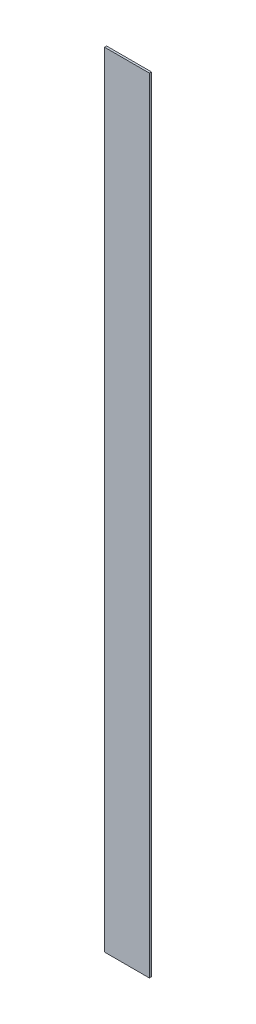
SolidWorks part; units mm, degrees
material "Cedar"
ref_plane "Front Plane" through (0, 0, 0) normal (0, 0, 1) x (1, 0, 0)
ref_plane "Top Plane" through (0, 0, 0) normal (0, 1, 0) x (1, 0, 0)
ref_plane "Right Plane" through (0, 0, 0) normal (1, 0, 0) x (0, 0, -1)
sketch "Sketch1" plane through (0, 0, 0) normal (0, 0, 1) x (1, 0, 0)
  line L0 (-43, -752) -> (43, -752)
  line L1 (43, -752) -> (43, 752)
  line L2 (43, 752) -> (-38, 752)
  line L3 (-80.1782, -752) -> (67.2915, -752) construction
  line L4 (-80.1782, -652) -> (67.2915, -652) construction
  line L5 (-80.1782, -552) -> (67.2915, -552) construction
  line L6 (-38, 752) -> (-43, 752)
  line L7 (-43, 752) -> (-43, -752)
  line L8 (-80.1782, -452) -> (67.2915, -452) construction
  line L9 (-80.1782, -352) -> (67.2915, -352) construction
  line L10 (-80.1782, -252) -> (67.2915, -252) construction
  line L11 (-80.1782, -152) -> (67.2915, -152) construction
  line L12 (-80.1782, -52) -> (67.2915, -52) construction
  line L13 (-80.1782, 48) -> (67.2915, 48) construction
  line L14 (-80.1782, 148) -> (67.2915, 148) construction
  line L15 (-80.1782, 248) -> (67.2915, 248) construction
  line L16 (-80.1782, 348) -> (67.2915, 348) construction
  line L17 (-80.1782, 448) -> (67.2915, 448) construction
  line L18 (-80.1782, 548) -> (67.2915, 548) construction
  line L19 (-80.1782, 648) -> (67.2915, 648) construction
  line L20 (-80.1782, 748) -> (67.2915, 748) construction
  line L21 (69.582, 752) -> (-94.7362, 752) construction
  line L22 (69.582, 652) -> (-94.7362, 652) construction
  line L23 (69.582, 552) -> (-94.7362, 552) construction
  line L24 (69.582, 452) -> (-94.7362, 452) construction
  line L25 (69.582, 352) -> (-94.7362, 352) construction
  line L26 (69.582, 252) -> (-94.7362, 252) construction
  line L27 (69.582, 152) -> (-94.7362, 152) construction
  line L28 (69.582, 52) -> (-94.7362, 52) construction
  line L29 (69.582, -48) -> (-94.7362, -48) construction
  line L30 (69.582, -148) -> (-94.7362, -148) construction
  line L31 (69.582, -248) -> (-94.7362, -248) construction
  line L32 (69.582, -348) -> (-94.7362, -348) construction
  line L33 (69.582, -448) -> (-94.7362, -448) construction
  line L34 (69.582, -548) -> (-94.7362, -548) construction
  line L35 (69.582, -648) -> (-94.7362, -648) construction
  line L36 (69.582, -748) -> (-94.7362, -748) construction
  dimension "D1" = 1504
  dimension "D3" = 16
  dimension "D2" = 16
extrude "Boss-Extrude1" add sketch "Sketch1" along normal blind 4
